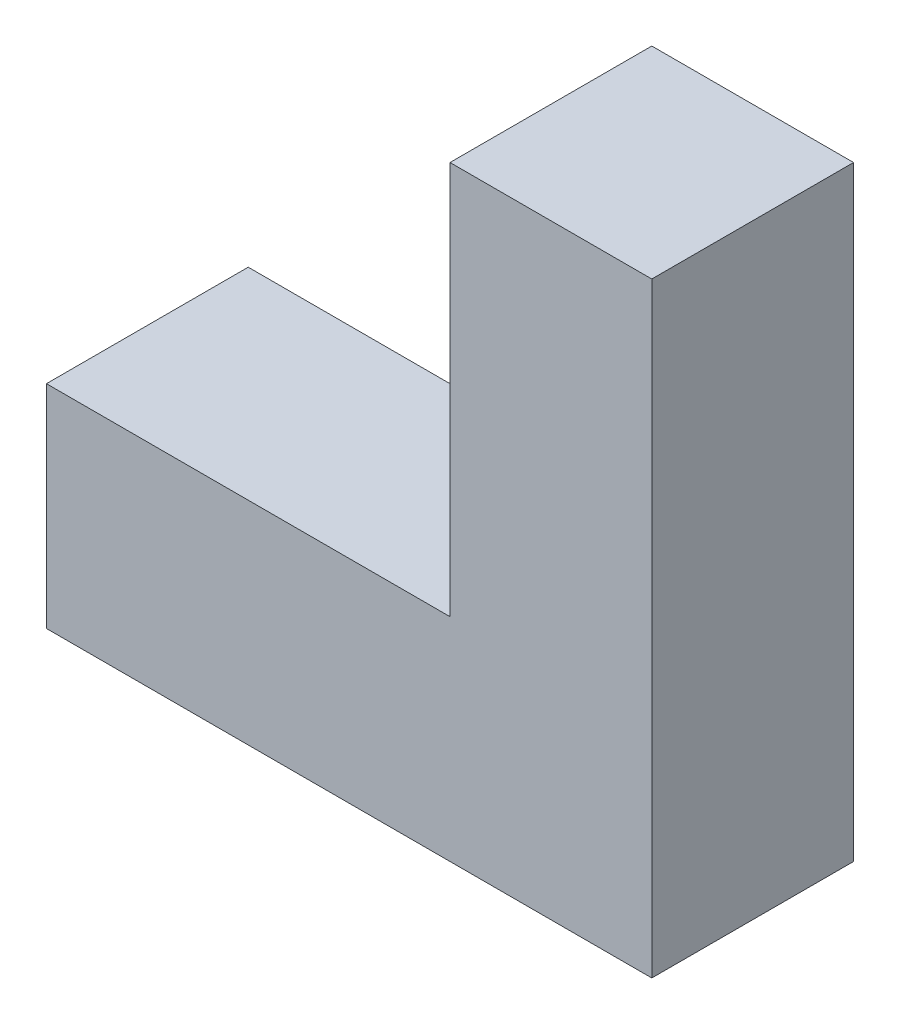
SolidWorks part; units mm, degrees
ref_plane "Front Plane" through (0, 0, 0) normal (0, 0, 1) x (1, 0, 0)
ref_plane "Top Plane" through (0, 0, 0) normal (0, 1, 0) x (1, 0, 0)
ref_plane "Right Plane" through (0, 0, 0) normal (1, 0, 0) x (0, 0, -1)
sketch "Sketch1" plane through (0, 0, 0) normal (0, 0, 1) x (1, 0, 0)
  line L1 (0, 0) -> (15, 0)
  line L2 (0, 15.7614) -> (0, 45)
  line L3 (0, 45) -> (15, 45)
  line L4 (15, 0) -> (15, 45)
  line L5 (0, 0) -> (-30, 0)
  line L7 (0, 15.7614) -> (-30, 15.7614)
  line L8 (-30, 0) -> (-30, 15.7614)
  dimension "D1" = 45
  dimension "D2" = 45
  dimension "D3" = 30
extrude "Boss-Extrude1" add sketch "Sketch1" along normal blind 15
